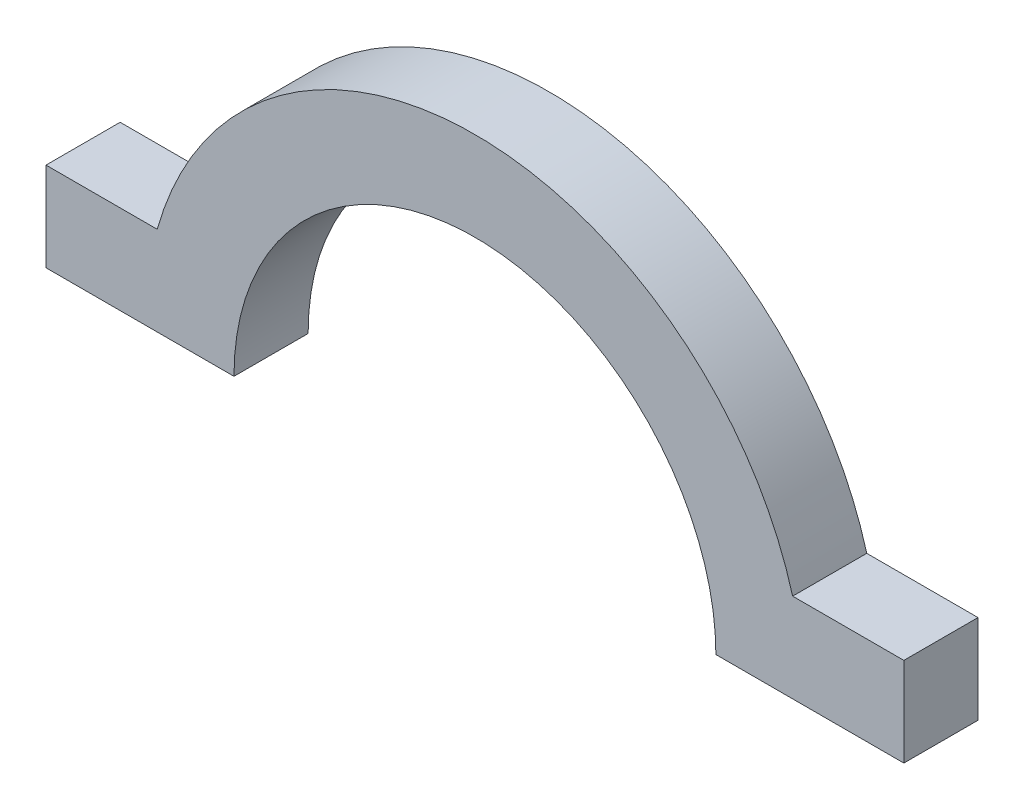
SolidWorks part; units mm, degrees
ref_plane "Front Plane" through (0, 0, 0) normal (0, 0, 1) x (1, 0, 0)
ref_plane "Top Plane" through (0, 0, 0) normal (0, 1, 0) x (1, 0, 0)
ref_plane "Right Plane" through (0, 0, 0) normal (1, 0, 0) x (0, 0, -1)
sketch "Sketch1" plane through (0, 0, 0) normal (0, 0, 1) x (1, 0, 0)
  line L0 (-60.2731, 0) -> (66.3995, 0) construction
  line L1 (-32.5, 0) -> (-57.8515, 0)
  line L2 (-57.8515, 0) -> (-57.8515, 12)
  line L3 (-57.8515, 12) -> (-42.8515, 12)
  line L4 (0, 53.4555) -> (0, -16.7626) construction
  line L5 (32.5, 0) -> (57.8515, 0)
  line L6 (57.8515, 0) -> (57.8515, 12)
  line L7 (57.8515, 12) -> (42.8515, 12)
  arc A0 (32.5, 0) -> (-32.5, 0) centre (0, 0) ccw
  arc A1 (42.8515, 12) -> (-42.8515, 12) centre (0, 0) ccw
  circle A2 centre (0, 0) radius 44.5 construction
  circle A3 centre (0, 0) radius 32.5 construction
  dimension "D1" = 65
  dimension "D3" = 15
  dimension "D4" = 12
  dimension "D2" = 12
extrude "Boss-Extrude1" add sketch "Sketch1" along normal blind 10
